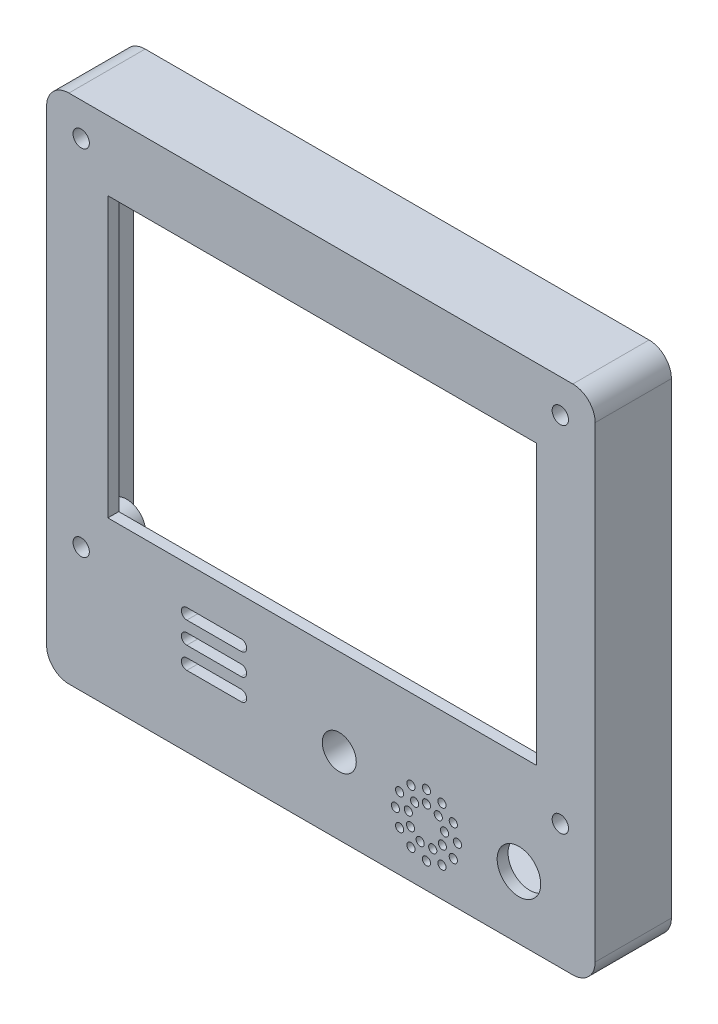
SolidWorks part; units mm, degrees
ref_plane "Front Plane" through (0, 0, 0) normal (0, 0, 1) x (1, 0, 0)
ref_plane "Top Plane" through (0, 0, 0) normal (0, 1, 0) x (1, 0, 0)
ref_plane "Right Plane" through (0, 0, 0) normal (1, 0, 0) x (0, 0, -1)
sketch "Sketch1" plane through (0, 0, 0) normal (0, 0, 1) x (1, 0, 0)
  line L1 (-50.375, -47) -> (50.375, -47)
  line L2 (-50.375, -47) -> (-50.375, 47)
  line L3 (-50.375, 47) -> (50.375, 47)
  line L4 (50.375, -47) -> (50.375, 47)
  line L5 (-50.375, -47) -> (50.375, 47) construction
  line L6 (-50.375, 47) -> (50.375, -47) construction
  point P0 (0, 0)
  dimension "D1" = 100.75
  dimension "D2" = 94
extrude "Boss-Extrude1" add sketch "Sketch1" along normal blind 14
shell "Shell1" thickness 2
sketch "Sketch2" plane through (0, 0, 12) normal (0, 0, -1) x (-1, 0, 0)
  line L0 (-43.975, 40.9) -> (43.975, 40.9) construction
  line L1 (43.975, 40.9) -> (43.975, -24.1) construction
  line L2 (43.975, -24.1) -> (-43.975, -24.1) construction
  line L3 (-43.975, -24.1) -> (-43.975, 40.9) construction
  line L4 (-48.375, 45) -> (48.375, 45) construction
  line L5 (-48.375, -45) -> (-48.375, 45) construction
  line L8 (48.375, -45) -> (-48.375, -45) construction
  line L9 (-50.375, -47) -> (-50.375, 47) construction
  circle A0 centre (-43.975, 40.9) radius 3.5
  circle A1 centre (-43.975, -24.1) radius 3.5
  circle A2 centre (43.975, 40.9) radius 3.5
  circle A3 centre (43.975, -24.1) radius 3.5
  circle A4 centre (-3.375, -33) radius 4
  dimension "D1" = 8
  dimension "D2" = 7
  dimension "D5" = 7
  dimension "D3" = 87.95
  dimension "D4" = 65
  dimension "D6" = 4.1
  dimension "D7" = 4.4
  dimension "D8" = 12
  dimension "D9" = 47
extrude "Boss-Extrude2" add sketch "Sketch2" along normal blind 6.3
sketch "Sketch3" plane through (0, 0, 14) normal (0, 0, 1) x (1, 0, 0)
  line L0 (-50.375, 47) -> (-50.375, -47) construction
  line L1 (-39.125, -17) -> (39.625, -17)
  line L2 (-39.125, -17) -> (-39.125, 34.25)
  line L3 (-39.125, 34.25) -> (39.625, 34.25)
  line L4 (39.625, -17) -> (39.625, 34.25)
  line L5 (-39.125, -17) -> (39.625, 34.25) construction
  line L6 (-39.125, 34.25) -> (39.625, -17) construction
  line L7 (50.375, 47) -> (-50.375, 47) construction
  line L8 (-44.025, 40.9) -> (43.975, 40.9) construction
  line L9 (43.975, 40.9) -> (43.975, -24.1) construction
  line L10 (-44.025, 40.9) -> (-44.025, -24.1) construction
  line L11 (-44.025, -24.1) -> (43.975, -24.1) construction
  line L12 (-24.625, -25) -> (-14.625, -25) construction
  line L13 (-24.625, -24) -> (-14.625, -24)
  line L14 (-24.625, -26) -> (-14.625, -26)
  line L15 (-24.625, -29) -> (-14.625, -29) construction
  line L16 (-24.625, -28) -> (-14.625, -28)
  line L17 (-24.625, -30) -> (-14.625, -30)
  line L18 (-24.625, -33) -> (-14.625, -33) construction
  line L19 (-24.625, -32) -> (-14.625, -32)
  line L20 (-24.625, -34) -> (-14.625, -34)
  line L21 (-50.375, -47) -> (50.375, -47) construction
  line L22 (-24.625, -33) -> (-24.625, -25) construction
  line L23 (50.375, -47) -> (50.375, 47) construction
  line L24 (50.375, -47) -> (50.375, 47) construction
  circle A0 centre (-44.025, 40.9) radius 1.5
  circle A1 centre (43.975, 40.9) radius 1.5
  circle A2 centre (43.975, -24.1) radius 1.5
  circle A3 centre (-44.025, -24.1) radius 1.5
  arc A5 (-24.625, -24) -> (-24.625, -26) centre (-24.625, -25) ccw
  arc A6 (-14.625, -26) -> (-14.625, -24) centre (-14.625, -25) ccw
  arc A7 (-24.625, -28) -> (-24.625, -30) centre (-24.625, -29) ccw
  arc A8 (-14.625, -30) -> (-14.625, -28) centre (-14.625, -29) ccw
  arc A9 (-24.625, -32) -> (-24.625, -34) centre (-24.625, -33) ccw
  arc A10 (-14.625, -34) -> (-14.625, -32) centre (-14.625, -33) ccw
  circle A11 centre (36.375, -35.5) radius 4
  circle A12 centre (3.375, -33) radius 3.125
  circle A13 centre (19.3883, -36.6212) radius 3.3782 construction
  circle A14 centre (19.3883, -33.243) radius 0.75
  circle A15 centre (19.3883, -36.6212) radius 3.3782 construction
  circle A16 centre (21.5598, -34.0333) radius 0.75
  circle A17 centre (19.3883, -36.6212) radius 3.3782 construction
  circle A18 centre (22.7152, -36.0346) radius 0.75
  circle A19 centre (19.3883, -36.6212) radius 3.3782 construction
  circle A20 centre (22.3139, -38.3103) radius 0.75
  circle A21 centre (19.3883, -36.6212) radius 3.3782 construction
  circle A22 centre (20.5437, -39.7957) radius 0.75
  circle A23 centre (19.3883, -36.6212) radius 3.3782 construction
  circle A24 centre (18.2328, -39.7957) radius 0.75
  circle A25 centre (19.3883, -36.6212) radius 3.3782 construction
  circle A26 centre (16.4626, -38.3103) radius 0.75
  circle A27 centre (19.3883, -36.6212) radius 3.3782 construction
  circle A28 centre (16.0614, -36.0346) radius 0.75
  circle A29 centre (19.3883, -36.6212) radius 3.3782 construction
  circle A30 centre (17.2168, -34.0333) radius 0.75
  circle A31 centre (19.3883, -36.6212) radius 5.6942 construction
  circle A32 centre (19.3883, -30.927) radius 0.75
  circle A33 centre (22.2354, -31.6899) radius 0.75
  circle A34 centre (24.3196, -33.7741) radius 0.75
  circle A35 centre (25.0825, -36.6212) radius 0.75
  circle A36 centre (24.3196, -39.4683) radius 0.75
  circle A37 centre (22.2354, -41.5525) radius 0.75
  circle A38 centre (19.3883, -42.3154) radius 0.75
  circle A39 centre (16.5412, -41.5525) radius 0.75
  circle A40 centre (14.4569, -39.4683) radius 0.75
  circle A41 centre (13.6941, -36.6212) radius 0.75
  circle A42 centre (14.4569, -33.7741) radius 0.75
  circle A43 centre (16.5412, -31.6899) radius 0.75
  point P0 (0.25, 8.625)
  point P17 (-19.625, -25)
  point P26 (-19.625, -29)
  point P33 (-19.625, -33)
  point P79 (19.3883, -36.6212)
  point P105 (19.3883, -36.6212)
  dimension "D21" = 8
  dimension "D24" = 6.25
  dimension "D25" = 1.5
  dimension "D27" = 1.5
  dimension "D29" = 3
  dimension "D1" = 78.75
  dimension "D2" = 51.25
  dimension "D3" = 11.25
  dimension "D4" = 12.75
  dimension "D5" = 6.4
  dimension "D6" = 6.1
  dimension "D7" = 88
  dimension "D8" = 65
  dimension "D9" = 2
  dimension "D10" = 2
  dimension "D11" = 2
  dimension "D12" = 10
  dimension "D13" = 10
  dimension "D14" = 10
  dimension "D15" = 4
  dimension "D16" = 4
  dimension "D17" = 14
  dimension "D18" = 25.75
  dimension "D19" = 14
  dimension "D20" = 11.5
  dimension "D22" = 14
  dimension "D23" = 47
  dimension "D26" = 9
  dimension "D28" = 12
extrude "Cut-Extrude1" cut sketch "Sketch3" against normal through all
fillet "Fillet1" radius 4.1 4 edges at (-50.375, -47, 7) (-50.375, 47, 7) (50.375, 47, 7) (50.375, -47, 7)
